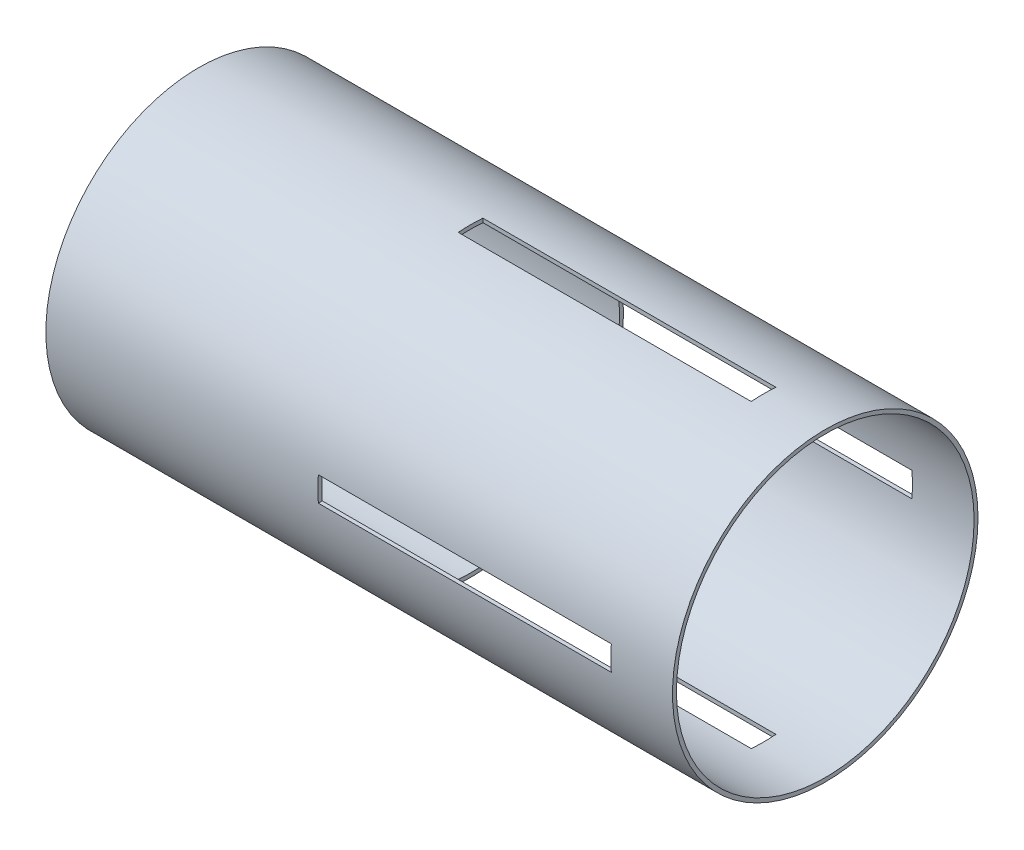
SolidWorks part; units mm, degrees
ref_plane "Front Plane" through (0, 0, 0) normal (0, 0, 1) x (1, 0, 0)
ref_plane "Top Plane" through (0, 0, 0) normal (0, 1, 0) x (1, 0, 0)
ref_plane "Right Plane" through (0, 0, 0) normal (1, 0, 0) x (0, 0, -1)
sketch "Sketch2" plane through (0, 0, 0) normal (1, 0, 0) x (0, 0, -1)
  circle A0 centre (0, 0) radius 48.26
  circle A1 centre (0, 0) radius 49.53
  point P3 (-42.8481, -47.9377)
  point P4 (0, 0)
  point P5 (0, 0)
  dimension "D1" = 99.06
  dimension "D2" = 1.27
extrude "Boss-Extrude1" add sketch "Sketch2" along normal blind 203.2 contours A1 A0
sketch "Sketch4" plane through (0, 0, 0) normal (0, 0, 1) x (1, 0, 0)
  line L0 (203.2, -49.53) -> (203.2, 49.53) construction
  line L1 (203.2, 49.53) -> (0, 49.53) construction
  line L2 (203.2, -49.53) -> (203.2, 49.53) construction
  line L3 (203.2, 49.53) -> (0, 49.53) construction
  line L4 (88.2, 49.53) -> (88.2, 45.53)
  line L5 (88.2, 45.53) -> (183.2, 45.53)
  line L6 (183.2, 45.53) -> (183.2, 49.53)
  line L7 (183.2, 49.53) -> (88.2, 49.53) construction
  line L8 (88.2, 49.53) -> (183.2, 49.53)
  dimension "D1" = 20
  dimension "D2" = 95
  dimension "D3" = 4
extrude "Cut-Extrude1" cut sketch "Sketch4" against normal mid plane 8
pattern_circular "CirPattern1" count 4 over 360 about axis through (0, 0, 0) along (1, 0, 0) of "Cut-Extrude1"
ref_plane "Plane1" through (132.312, 7.5, -47.2079) normal (1, 0, 0) x (0, 0, -1)
